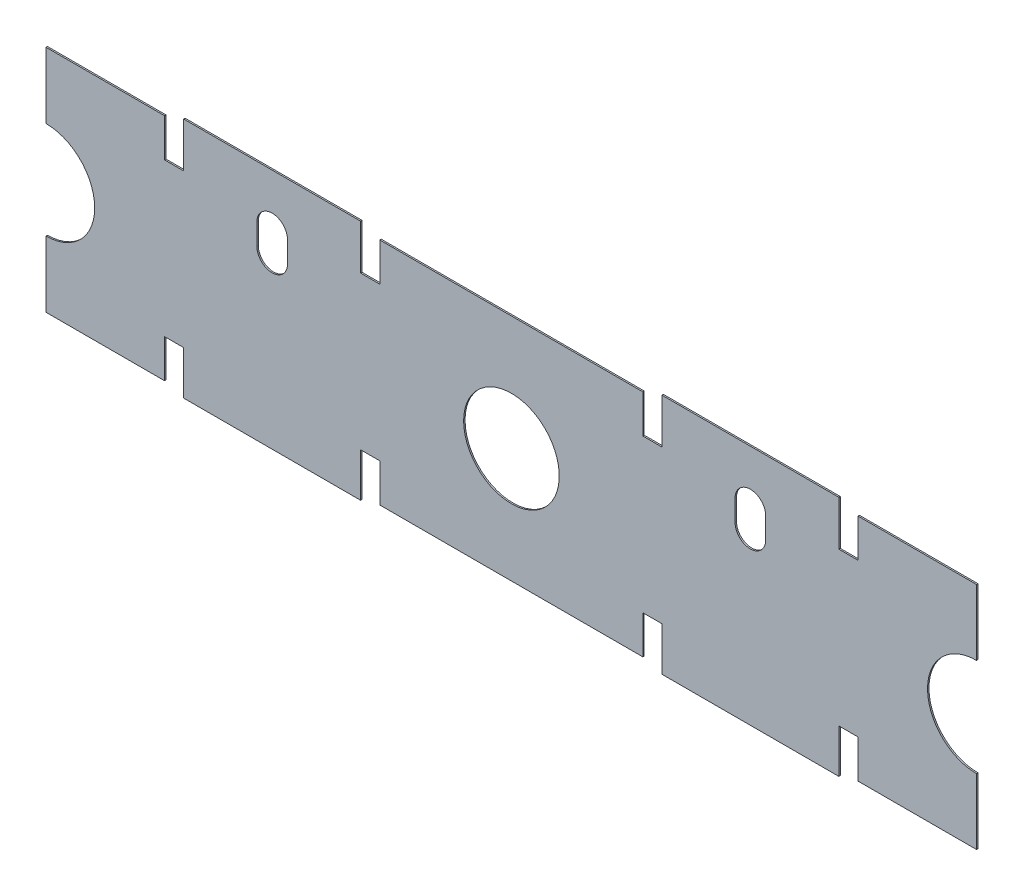
SolidWorks part; units mm, degrees
ref_plane "Спереди" through (0, 0, 0) normal (0, 0, 1) x (1, 0, 0)
ref_plane "Сверху" through (0, 0, 0) normal (0, 1, 0) x (1, 0, 0)
ref_plane "Справа" through (0, 0, 0) normal (1, 0, 0) x (0, 0, -1)
ref_plane "Плоскость1" through (0, 0, 0) normal (0, 0, -1) x (-1, 0, 0)
sketch "Эскиз1" plane through (0, 0, 0) normal (0, 0, -1) x (-1, 0, 0)
  line L0 (-94.25, 76.7) -> (-94.25, 72)
  line L1 (-94.25, 72) -> (-96.25, 72)
  line L2 (-96.25, 72) -> (-96.25, 76)
  line L3 (-96.25, 76) -> (-108.65, 76)
  line L4 (-108.65, 76) -> (-108.65, 69.127)
  line L7 (-85, 76.7) -> (-85, 72.8) construction
  line L8 (-60, 76) -> (-60, 50076) construction
  line L9 (-33.4, 69) -> (-33.4, 71.2)
  line L10 (-36.6, 71.2) -> (-36.6, 69)
  line L32 (-108.65, 58.873) -> (-108.65, 52)
  line L33 (-108.65, 52) -> (-96.25, 52)
  line L34 (-96.25, 52) -> (-96.25, 56)
  line L35 (-96.25, 56) -> (-94.25, 56)
  line L36 (-94.25, 56) -> (-94.25, 51.425)
  line L37 (-94.25, 51.425) -> (-75.75, 51.425)
  line L38 (-75.75, 51.425) -> (-75.75, 56)
  line L39 (-75.75, 56) -> (-73.75, 56)
  line L40 (-73.75, 56) -> (-73.75, 52)
  line L41 (-73.75, 52) -> (-46.25, 52)
  line L42 (-46.25, 52) -> (-46.25, 56)
  line L43 (-46.25, 56) -> (-44.25, 56)
  line L44 (-44.25, 56) -> (-44.25, 51.425)
  line L45 (-44.25, 51.425) -> (-25.75, 51.425)
  line L46 (-25.75, 51.425) -> (-25.75, 56)
  line L47 (-25.75, 56) -> (-23.75, 56)
  line L48 (-23.75, 56) -> (-23.75, 52)
  line L49 (-23.75, 52) -> (-11.35, 52)
  line L50 (-11.35, 52) -> (-11.35, 58.91)
  line L78 (-11.35, 69.09) -> (-11.35, 76)
  line L79 (-11.35, 76) -> (-23.75, 76)
  line L80 (-23.75, 76) -> (-23.75, 72)
  line L81 (-23.75, 72) -> (-25.75, 72)
  line L82 (-25.75, 72) -> (-25.75, 76.7)
  line L83 (-25.75, 76.7) -> (-44.25, 76.7)
  line L84 (-44.25, 76.7) -> (-44.25, 72)
  line L85 (-44.25, 72) -> (-46.25, 72)
  line L86 (-46.25, 72) -> (-46.25, 76)
  line L87 (-46.25, 76) -> (-73.75, 76)
  line L88 (-73.75, 76) -> (-73.75, 72)
  line L89 (-73.75, 72) -> (-75.75, 72)
  line L90 (-75.75, 72) -> (-75.75, 76.7)
  line L91 (-75.75, 76.7) -> (-94.25, 76.7)
  line L147 (-83.4, 71.2) -> (-83.4, 69)
  line L163 (-86.6, 69) -> (-86.6, 71.2)
  circle A0 centre (-60.0171, 64) radius 5
  arc A1 (-108.65, 58.873) -> (-108.65, 69.127) centre (-108.65, 64) ccw
  arc A2 (-11.35, 69.09) -> (-11.35, 58.91) centre (-11.35, 64) ccw
  arc A3 (-86.6, 69) -> (-83.4, 69) centre (-85, 69) ccw
  arc A4 (-86.6, 71.2) -> (-83.4, 71.2) centre (-85, 71.2) cw
  arc A7 (-33.4, 71.2) -> (-36.6, 71.2) centre (-35, 71.2) ccw
  arc A8 (-33.4, 69) -> (-36.6, 69) centre (-35, 69) cw
  point P14 (-85, 72.8)
  point P17 (-60, 76)
  dimension "D2" = 1.6
  dimension "D1" = 10
  dimension "D3" = 3.9
  dimension "D4" = 2.2
  dimension "D5" = 12
  dimension "D6" = 48.6329
extrude "Бобышка-Вытянуть1" add sketch "Эскиз1" against normal blind 0.15
